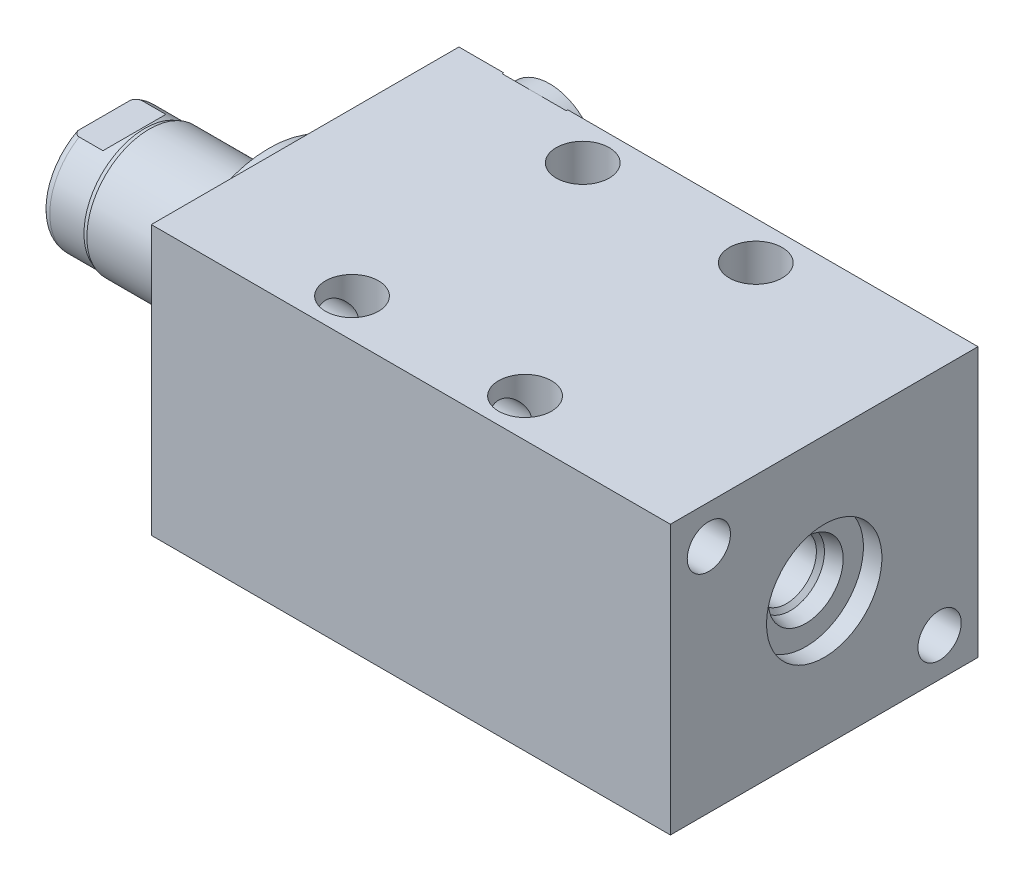
SolidWorks part; units mm, degrees
material "Alloy Steel"
ref_plane "Front Plane" through (0, 0, 0) normal (0, 0, 1) x (1, 0, 0)
ref_plane "Top Plane" through (0, 0, 0) normal (0, 1, 0) x (1, 0, 0)
ref_plane "Right Plane" through (0, 0, 0) normal (1, 0, 0) x (0, 0, -1)
ref_plane "Plane1" through (0, 0, 0) normal (1, 0, 0) x (0, 0, -1)
sketch "Sketch1" plane through (0, 0, 0) normal (1, 0, 0) x (0, 0, -1)
  line L0 (-25.4, 22.225) -> (25.4, 22.225)
  line L1 (25.4, 22.225) -> (25.4, -22.225)
  line L2 (25.4, -22.225) -> (-25.4, -22.225)
  line L3 (-25.4, -22.225) -> (-25.4, 22.225)
  line L4 (0, -24.4475) -> (0, 24.4475) construction
  dimension "D1" = 44.45
  dimension "D2" = 22.225
  dimension "D3" = 50.8
extrude "Extrude1" add sketch "Sketch1" along normal blind 85.725
ref_plane "Plane12" through (0, 14.3002, 0) normal (0, 1, 0) x (-1, 0, 0)
sketch "S2D0002" plane through (0, 14.3002, 0) normal (0, 1, 0) x (-1, 0, 0)
  line L0 (-18.8849, -25.146) -> (-22.225, -25.146)
  line L1 (-18.8849, -25.146) -> (-18.3423, -22.5933)
  line L2 (-18.3423, -22.5933) -> (-17.6784, -21.9294)
  line L3 (-17.6784, -21.9294) -> (-17.6784, -11.176)
  line L4 (-17.6784, -11.176) -> (-12.7, -11.176)
  line L5 (-12.7, -11.176) -> (-12.7, -25.4)
  line L6 (-12.7, -19.1384) -> (-12.7, 0.6985) construction
  line L7 (0, -25.4) -> (0, 25.4) construction
  line L8 (-22.225, -25.4) -> (-22.225, -25.146)
  line L9 (-85.725, -25.4) -> (0, -25.4) construction
  line L10 (-22.225, -25.4) -> (-12.7, -25.4)
  dimension "D1" = 14.224
  dimension "D2" = 12.7
  dimension "D3" = 9.9568
  dimension "D4" = 45
  dimension "D5" = 12.3698
  dimension "D6" = 12
  dimension "D7" = 2.5527
  dimension "D8" = 0.254
  dimension "D9" = 19.05
revolve "Cut-Revolve1" cut sketch "S2D0002" angle 360 about L6
ref_plane "Plane3" through (41.148, 0, -25.146) normal (0, 1, 0) x (1, 0, 0)
sketch "Sketch3" plane through (41.148, 0, -25.146) normal (0, 1, 0) x (1, 0, 0)
  line L0 (34.8869, 0) -> (38.227, 0)
  line L1 (34.8869, 0) -> (34.3443, -2.5527)
  line L2 (34.3443, -2.5527) -> (33.6804, -3.2166)
  line L3 (33.6804, -3.2166) -> (33.6804, -13.97)
  line L4 (33.6804, -13.97) -> (28.702, -13.97)
  line L5 (28.702, -13.97) -> (28.702, 0.254)
  line L6 (28.702, -21.9564) -> (28.702, 0.6985) construction
  line L7 (-41.148, 0.254) -> (-41.148, -50.546) construction
  line L8 (38.227, 0.254) -> (38.227, 0)
  line L9 (44.577, 0.254) -> (-23.1638, 0.254) construction
  line L10 (38.227, 0.254) -> (28.702, 0.254)
  dimension "D1" = 14.224
  dimension "D2" = 69.85
  dimension "D3" = 9.9568
  dimension "D4" = 45
  dimension "D5" = 12
  dimension "D6" = 12.3698
  dimension "D7" = 2.5527
  dimension "D8" = 0.254
  dimension "D9" = 19.05
revolve "Cut-Revolve2" cut sketch "Sketch3" angle 360 about L6
ref_plane "Plane4" through (53.975, 0, 0) normal (0, 0, 1) x (0, -1, 0)
sketch "Sketch4" plane through (53.975, 0, 0) normal (0, 0, 1) x (0, -1, 0)
  line L0 (6.1849, 28.702) -> (9.525, 28.702)
  line L1 (6.1849, 28.702) -> (5.6423, 26.1493)
  line L2 (5.6423, 26.1493) -> (4.9784, 25.4854)
  line L3 (4.9784, 25.4854) -> (4.9784, 17.3482)
  line L4 (4.9784, 17.3482) -> (0, 17.3482)
  line L5 (0, 17.3482) -> (0, 31.75)
  line L6 (0, -15.0954) -> (0, 0.5677) construction
  line L7 (0, 31.75) -> (9.525, 31.75)
  line L9 (-22.225, 31.75) -> (22.225, 31.75) construction
  line L10 (9.525, 31.75) -> (9.525, 28.702)
  dimension "D1" = 11.3538
  dimension "D2" = 9.9568
  dimension "D3" = 3.048
  dimension "D4" = 19.05
  dimension "D5" = 2.5527
  dimension "D6" = 12
  dimension "D7" = 45
  dimension "D8" = 12.3698
revolve "Cut-Revolve3" cut sketch "Sketch4" angle 360 about L6
sketch "Sketch5" plane through (0, 0, 0) normal (-1, 0, 0) x (0, 0, 1)
  circle A0 centre (0, 0) radius 17.4625
  dimension "D1" = 34.925
extrude "Extrude2" add sketch "Sketch5" along normal blind 5.969
ref_plane "Plane5" through (0, 0, 0) normal (0, -1, 0) x (0, 0, 1)
sketch "Sketch6" plane through (0, 0, 0) normal (0, -1, 0) x (0, 0, 1)
  line L0 (0, 5.969) -> (-10.3187, 5.969)
  line L1 (-10.3187, 5.969) -> (-10.3187, 33.147)
  line L2 (-10.3187, 33.147) -> (0, 33.147)
  line L3 (0, 33.147) -> (0, 5.969)
  line L4 (0, -5.7546) -> (0, 21.1709) construction
  line L5 (17.4625, 5.969) -> (-17.4625, 5.969) construction
  line L6 (25.4, -85.725) -> (-25.4, -85.725) construction
  dimension "D1" = 118.872
  dimension "D2" = 20.6375
revolve "Revolve1" add sketch "Sketch6" angle 360 about L4
ref_plane "Plane6" through (-18.5113, 3.2639, 0) normal (0, 0, 1) x (0, 1, 0)
sketch "S2D0001" plane through (-18.5113, 3.2639, 0) normal (0, 0, 1) x (0, 1, 0)
  line L0 (0, 12.7) -> (0, -0.2995)
  line L1 (0, -0.2995) -> (-3.2639, -0.2995)
  line L2 (1.1176, 14.6357) -> (-3.2639, 14.6357)
  line L3 (-3.2639, 14.6357) -> (-3.2639, -0.2995)
  line L4 (0, 12.7) -> (1.1176, 14.6357)
  line L5 (-3.2639, -18.5113) -> (-3.2639, 2.765) construction
  line L6 (7.0549, 14.6357) -> (-13.5826, 14.6357) construction
  dimension "D1" = 30
  dimension "D2" = 8.763
  dimension "D3" = 6.5278
  dimension "D4" = 14.9352
revolve "Cut-Revolve4" cut sketch "S2D0001" angle 360 about L5
ref_plane "Plane7" through (0, 0, 0) normal (0, 1, 0) x (0, 0, -1)
sketch "Sketch8" plane through (0, 0, 0) normal (0, 1, 0) x (0, 0, -1)
  line L0 (-10.3187, 25.7302) -> (-10.033, 26.4922)
  line L1 (-10.033, 26.4922) -> (-10.033, 32.131)
  line L2 (0, 12.6594) -> (0, 20.8178) construction
  line L3 (-10.3187, 25.7302) -> (-10.3187, 33.147)
  line L4 (-9.6449, 33.147) -> (-10.3187, 33.147)
  line L5 (10.3187, 33.147) -> (-10.3187, 33.147) construction
  line L6 (-10.3187, 33.147) -> (-10.3187, 5.969) construction
  arc A0 (-9.6449, 33.147) -> (-10.033, 32.131) centre (-8.509, 32.131) ccw
  dimension "D2" = 1.524
  dimension "D1" = 20.066
  dimension "D3" = 1.016
  dimension "D4" = 0.762
  dimension "D5" = 6.6548
revolve "Cut-Revolve5" cut sketch "Sketch8" angle 360 about L2
ref_plane "Plane11" through (0, 0, 0) normal (0, 0, -1) x (0, -1, 0)
sketch "Sketch12" plane through (0, 0, 0) normal (0, 0, -1) x (0, -1, 0)
  line L0 (8.5852, 33.147) -> (8.5852, 28.194)
  line L1 (8.5852, 28.194) -> (10.033, 26.7462)
  line L2 (-8.5852, 33.147) -> (-8.5852, 28.194)
  line L3 (-8.5852, 28.194) -> (-10.033, 26.7462)
  line L4 (8.5852, 33.147) -> (10.033, 33.147)
  line L5 (0, 13.7262) -> (0, 20.767) construction
  line L6 (-10.033, 26.7462) -> (-10.033, 33.147)
  line L7 (9.6449, 33.147) -> (-9.6449, 33.147) construction
  line L8 (10.033, 26.4922) -> (10.033, 32.131) construction
  line L9 (10.033, 26.7462) -> (10.033, 33.147)
  line L10 (-8.5852, 33.147) -> (-10.033, 33.147)
  dimension "D1" = 17.1704
  dimension "D2" = 4.953
  dimension "D3" = 45
extrude "Cut-Extrude4" cut sketch "Sketch12" against normal mid plane 60.96
sketch "Sketch13" plane through (0, 0, -25.146) normal (0, 0, -1) x (-1, 0, 0)
  circle A0 centre (-12.7, 14.3002) radius 7.874
  circle A1 centre (-12.7, 14.3002) radius 6.1849 construction
  dimension "D1" = 15.748
extrude "Extrude3" add sketch "Sketch13" along normal blind 2.54
hole_wizard "Hole1" positions "Sketch15" profile "Sketch14" legacy end condition up to next
sketch "Sketch15" plane through (0, 0, 0) normal (-1, 0, 0) x (0, 0, 1)
  line L0 (0, 0) -> (-29.9914, 0) construction
  line L1 (0, 0) -> (0, 25.7648) construction
  point P0 (-19.05, -15.875)
  point P11 (19.05, 15.875)
  dimension "D1" = 15.875
  dimension "D2" = 19.05
  dimension "D3" = 31.75
  dimension "D4" = 38.1
sketch "Sketch14" plane through (0, -15.875, -19.05) normal (0, 1, 0) x (0, 0, 1)
  line L0 (0, 0) -> (0, 85.725)
  line L1 (0, 85.725) -> (3.5687, 85.725)
  line L2 (3.5687, 85.725) -> (3.5687, 0)
  line L3 (3.5687, 0) -> (0, 0)
  line L4 (0, 110) -> (0, -10) construction
  dimension "Diameter" = 7.1374
  dimension "Depth" = 85.725
hole_wizard "Hole2" positions "Sketch17" profile "Sketch16" legacy
sketch "Sketch17" plane through (0, 22.225, 0) normal (0, 1, 0) x (-1, 0, 0)
  line L0 (0, 0) -> (-59.3363, 0) construction
  line L1 (0, -25.4) -> (0, 25.4) construction
  point P0 (-26.797, -19.05)
  point P9 (-26.797, 19.05)
  dimension "D1" = 38.1
  dimension "D2" = 26.797
sketch "Sketch16" plane through (26.797, 22.225, -19.05) normal (1, 0, 0) x (0, 0, 1)
  line L0 (0, 0) -> (0, 44.45)
  line L1 (0, 44.45) -> (4.3688, 44.45)
  line L2 (4.3688, 44.45) -> (4.3688, 0)
  line L3 (4.3688, 0) -> (0, 0)
  line L4 (0, 110) -> (0, -10) construction
  dimension "Diameter" = 8.7376
  dimension "Depth" = 44.45
pattern_linear "LPattern1" count 2 spacing 28.575 along (1, 0, 0) of "Hole2"
